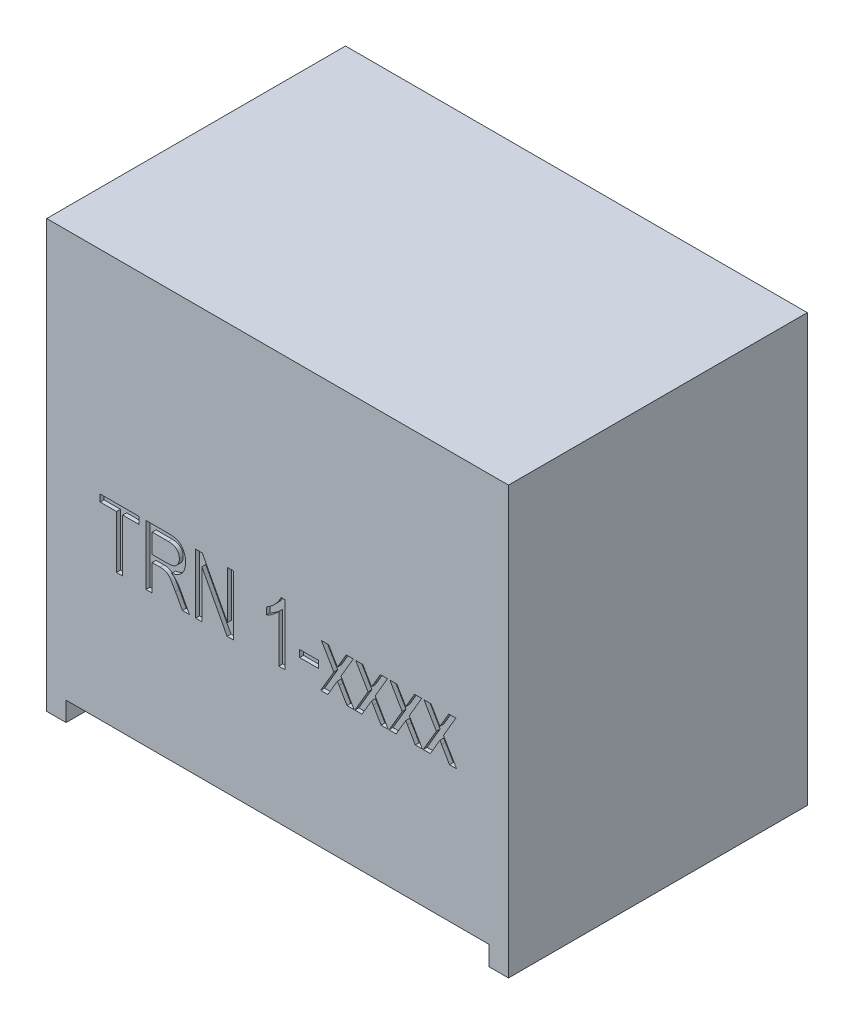
SolidWorks part; units mm, degrees
ref_plane "Front Plane" through (0, 0, 0) normal (0, 0, 1) x (1, 0, 0)
ref_plane "Top Plane" through (0, 0, 0) normal (0, 1, 0) x (1, 0, 0)
ref_plane "Right Plane" through (0, 0, 0) normal (1, 0, 0) x (0, 0, -1)
sketch "Sketch1" plane through (0, 0, 0) normal (0, 1, 0) x (1, 0, 0)
  line L1 (-5.95, 3.85) -> (5.95, 3.85)
  line L2 (-5.95, 3.85) -> (-5.95, -3.85)
  line L3 (-5.95, -3.85) -> (5.95, -3.85)
  line L4 (5.95, 3.85) -> (5.95, -3.85)
  line L5 (-5.95, 3.85) -> (5.95, -3.85) construction
  line L6 (-5.95, -3.85) -> (5.95, 3.85) construction
  point P0 (0, 0)
  dimension "D1" = 11.9
  dimension "D2" = 7.7
extrude "Boss-Extrude1" add sketch "Sketch1" along normal blind 11
sketch "Sketch2" plane through (0, 0, 0) normal (0, -1, 0) x (1, 0, 0)
  line L0 (-5.95, 3.85) -> (5.95, 3.85) construction
  line L1 (-5.45, -3.85) -> (5.45, -3.85)
  line L2 (-5.45, -3.85) -> (-5.45, 3.85)
  line L3 (-5.45, 3.85) -> (5.45, 3.85)
  line L4 (5.45, -3.85) -> (5.45, 3.85)
  line L5 (-5.45, -3.85) -> (5.45, 3.85) construction
  line L6 (-5.45, 3.85) -> (5.45, -3.85) construction
  point P0 (0, 0)
  dimension "D1" = 10.9
extrude "Cut-Extrude1" cut sketch "Sketch2" against normal blind 0.5
ref_plane "Plane1" through (0, 0, 0.15) normal (0, 0, 1) x (1, 0, 0)
sketch "Sketch3" plane through (0, 0, 3.85) normal (0, 0, 1) x (1, 0, 0)
  line L0 (-4.95, 4) -> (4.95, 4) construction
  line L1 (-5.95, 11) -> (5.95, 11) construction
  line L2 (-5.95, 11) -> (-5.95, 0) construction
  line L3 (5.95, 11) -> (5.95, 0) construction
  text T0 "TRN 1-xxxx" font "Arial Narrow" height in points 6
  dimension "D1" = 7
  dimension "D2" = 1
  dimension "D3" = 1
extrude "Cut-Extrude2" cut sketch "Sketch3" against normal blind 0.1
